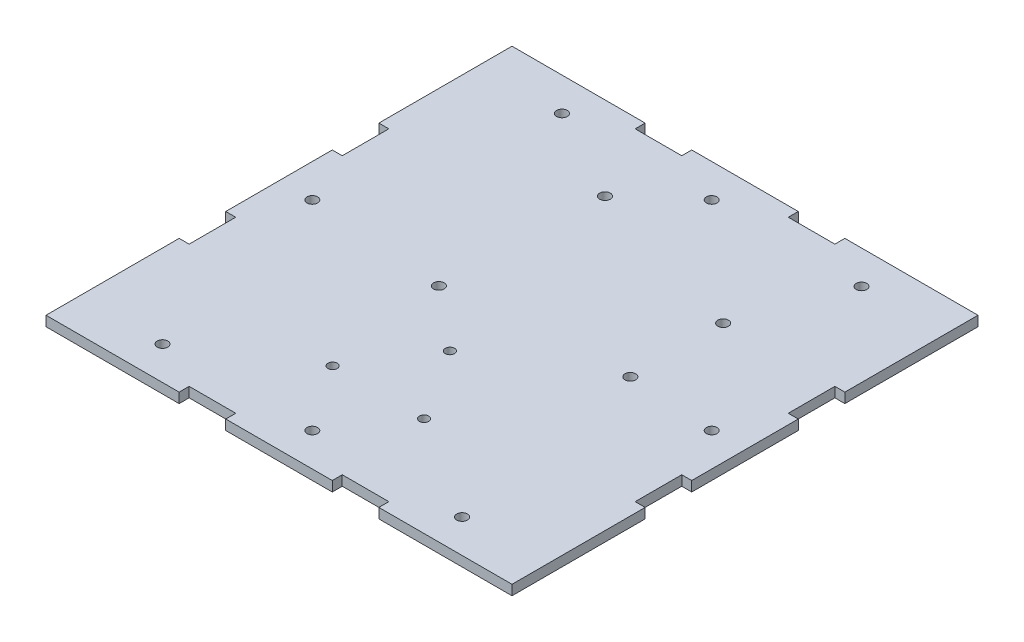
SolidWorks part; units mm, degrees
ref_plane "Front Plane" through (0, 0, 0) normal (0, 0, 1) x (1, 0, 0)
ref_plane "Top Plane" through (0, 0, 0) normal (0, 1, 0) x (1, 0, 0)
ref_plane "Right Plane" through (0, 0, 0) normal (1, 0, 0) x (0, 0, -1)
sketch "Sketch2" plane through (0, 0, 0) normal (0, 1, 0) x (1, 0, 0)
  line L0 (-70, 70) -> (70, -70) construction
  line L1 (-70, 70) -> (70, 70)
  line L2 (-70, 70) -> (-70, -70)
  line L3 (-70, -70) -> (70, -70)
  line L4 (70, 70) -> (70, -70)
  line L5 (70, 70) -> (-70, -70) construction
  line L6 (-0.0302, -29.4237) -> (-0.0302, -47.5058) construction
  line L7 (-50, 50) -> (50, -50) construction
  line L8 (50, 50) -> (-50, 50)
  line L9 (50, 50) -> (50, -50)
  line L10 (50, -50) -> (-50, -50)
  line L11 (-50, 50) -> (-50, -50)
  line L12 (50, 50) -> (-50, -50) construction
  line L13 (-18.6116, -3.3508) -> (-18.6116, 44.9492) construction
  line L14 (33.7884, 1.7492) -> (22.0917, 1.7492)
  line L15 (-18.6116, -3.3508) -> (22.0917, -3.3508)
  line L16 (22.0917, -3.3508) -> (22.0917, 1.7492)
  line L17 (0, 70) -> (0, -70) construction
  line L18 (-70, 0) -> (70, 0) construction
  line L19 (0, 70) -> (0, 50) construction
  line L20 (-50, 0) -> (-70, 0) construction
  line L21 (0, -50) -> (0, -70) construction
  line L22 (50, 0) -> (70, 0) construction
  line L23 (-45, 70) -> (-45, -70) construction
  line L24 (45, 70) -> (45, -70) construction
  line L25 (-45, 50) -> (-45, 70) construction
  line L26 (45, 50) -> (45, 70) construction
  line L27 (-45, -50) -> (-45, -70) construction
  line L28 (45, -50) -> (45, -70) construction
  circle A3 centre (-17.0116, 44.9492) radius 1.6
  circle A4 centre (-18.6116, -3.3508) radius 1.6
  circle A5 centre (33.7884, 29.6492) radius 1.6
  circle A6 centre (33.7884, 1.7492) radius 1.6
  circle A10 centre (0, 60) radius 1.6
  circle A11 centre (-60, 0) radius 1.6
  circle A12 centre (0, -60) radius 1.6
  circle A13 centre (60, 0) radius 1.6
  circle A14 centre (-45, 60) radius 1.6
  circle A15 centre (45, 60) radius 1.6
  circle A16 centre (-45, -60) radius 1.6
  circle A17 centre (45, -60) radius 1.6
  circle A18 centre (-0.0302, -18.6237) radius 1.4
  circle A19 centre (-13.7802, -40.1237) radius 1.4
  circle A20 centre (13.7198, -40.1237) radius 1.4
  point P12 (0, 0)
  point P18 (0, 0)
  point P40 (0, 60)
  point P44 (-60, 0)
  point P49 (0, -60)
  point P54 (60, 0)
  point P63 (-45, 60)
  point P68 (45, 60)
  point P73 (-45, -60)
  point P78 (45, -60)
  dimension "D3" = 25
  dimension "D9" = 3.2
  dimension "D11" = 2.8
  dimension "D1" = 140
  dimension "D2" = 100
  dimension "D4" = 50.8
  dimension "D5" = 27.9
  dimension "D6" = 5.1
  dimension "D7" = 48.3
  dimension "D8" = 40.7033
  dimension "D10" = 25
extrude "Boss-Extrude2" add sketch "Sketch2" along normal blind 3
sketch "Sketch3" plane through (0, 3, 0) normal (0, 1, 0) x (1, 0, 0)
  line L0 (30, -70) -> (30, -67)
  line L1 (-70, -70) -> (70, -70) construction
  line L2 (30, -67) -> (16, -67)
  line L3 (16, -67) -> (16, -70)
  line L4 (16, -70) -> (30, -70)
  line L5 (70, 70) -> (70, -70) construction
  line L6 (-1.65, 0) -> (1.65, 0) construction
  line L7 (16, 67) -> (16, 70)
  line L8 (30, 67) -> (16, 67)
  line L9 (30, 70) -> (30, 67)
  line L10 (16, 70) -> (30, 70)
  line L11 (0, -1.65) -> (0, 1.65) construction
  line L12 (-30, 67) -> (-16, 67)
  line L13 (-30, 70) -> (-30, 67)
  line L14 (-16, 70) -> (-30, 70)
  line L15 (-16, 67) -> (-16, 70)
  line L16 (-16, -67) -> (-16, -70)
  line L17 (-30, -67) -> (-16, -67)
  line L18 (-30, -70) -> (-30, -67)
  line L19 (-16, -70) -> (-30, -70)
  line L20 (70, -30) -> (67, -30)
  line L21 (67, -30) -> (67, -16)
  line L22 (67, -16) -> (70, -16)
  line L23 (70, -16) -> (70, -30)
  line L24 (67, 16) -> (70, 16)
  line L25 (67, 30) -> (67, 16)
  line L26 (70, 30) -> (67, 30)
  line L27 (70, 16) -> (70, 30)
  line L28 (-67, 30) -> (-67, 16)
  line L29 (-70, 30) -> (-67, 30)
  line L30 (-70, 16) -> (-70, 30)
  line L31 (-67, 16) -> (-70, 16)
  line L32 (-67, -16) -> (-70, -16)
  line L33 (-67, -30) -> (-67, -16)
  line L34 (-70, -30) -> (-67, -30)
  line L35 (-70, -16) -> (-70, -30)
  dimension "D1" = 3
  dimension "D2" = 14
  dimension "D3" = 40
  dimension "D4" = 3
  dimension "D5" = 14
  dimension "D6" = 40
extrude "Cut-Extrude1" cut sketch "Sketch3" against normal blind 10
